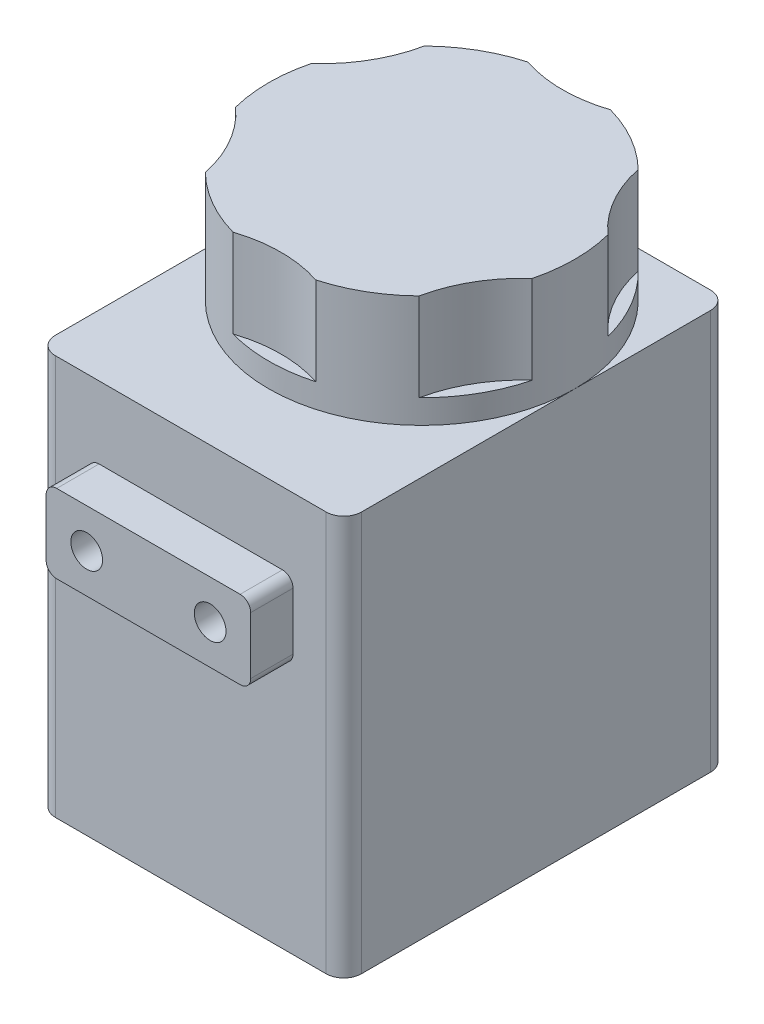
SolidWorks part; units mm, degrees
material "PE High Density"
ref_plane "Front Plane" through (0, 0, 0) normal (0, 0, 1) x (1, 0, 0)
ref_plane "Top Plane" through (0, 0, 0) normal (0, 1, 0) x (1, 0, 0)
ref_plane "Right Plane" through (0, 0, 0) normal (1, 0, 0) x (0, 0, -1)
sketch "Sketch1" plane through (0, 0, 0) normal (0, 1, 0) x (1, 0, 0)
  line L1 (0, 0) -> (22.0472, 0)
  line L2 (0, 0) -> (0, 27.686)
  line L3 (0, 27.686) -> (22.0472, 27.686)
  line L4 (22.0472, 0) -> (22.0472, 27.686)
  dimension "D1" = 22.0472
  dimension "D2" = 27.686
extrude "Boss-Extrude1" add sketch "Sketch1" along normal blind 28.8036
sketch "Sketch2" plane through (0, 0, 0) normal (0, 0, 1) x (1, 0, 0)
  line L0 (0, 20.8026) -> (22.0472, 20.8026) construction
  line L2 (0, 28.8036) -> (0, 0) construction
  line L3 (22.0472, 28.8036) -> (22.0472, 0) construction
  line L4 (0, 28.8036) -> (22.0472, 28.8036) construction
  line L6 (3.6576, 17.9832) -> (18.3896, 17.9832)
  line L7 (3.6576, 17.9832) -> (3.6576, 23.622)
  line L8 (3.6576, 23.622) -> (18.3896, 23.622)
  line L9 (18.3896, 17.9832) -> (18.3896, 23.622)
  line L10 (3.6576, 17.9832) -> (18.3896, 23.622) construction
  line L11 (3.6576, 23.622) -> (18.3896, 17.9832) construction
  point P8 (11.0236, 20.8026)
  dimension "D1" = 8.001
  dimension "D2" = 14.732
  dimension "D3" = 5.6388
extrude "Boss-Extrude2" add sketch "Sketch2" along normal blind 3.048
sketch "Sketch3" plane through (0, 28.8036, 0) normal (0, 1, 0) x (1, 0, 0)
  line L0 (0, 16.637) -> (22.0472, 16.637) construction
  line L1 (0, 27.686) -> (0, 0) construction
  line L2 (22.0472, 0) -> (22.0472, 27.686) construction
  line L3 (22.0472, 27.686) -> (0, 27.686) construction
  circle A0 centre (11.0236, 16.637) radius 11.0236
  dimension "D1" = 11.049
extrude "Boss-Extrude3" add sketch "Sketch3" along normal blind 8.0772
sketch "Sketch4" plane through (0, 36.8808, 0) normal (0, 1, 0) x (1, 0, 0)
  line L0 (11.0236, 27.6606) -> (11.0236, 36.2966) construction
  line L1 (8.1026, 32.307) -> (8.1026, 23.5851) construction
  arc A0 (22.0472, 16.637) -> (0, 16.637) centre (11.0236, 16.637) ccw construction
  circle A1 centre (11.0236, 36.2966) radius 9.525
  circle A2 centre (28.0493, 26.4668) radius 9.525
  circle A3 centre (28.0493, 6.8072) radius 9.525
  circle A4 centre (11.0236, -3.0226) radius 9.525
  circle A5 centre (-6.0021, 6.8072) radius 9.525
  circle A6 centre (-6.0021, 26.4668) radius 9.525
  point P22 (11.0236, 16.637)
  dimension "D2" = 19.05
  dimension "D1" = 2.921
  dimension "D3" = 8.636
  dimension "D4" = 6
extrude "Cut-Extrude1" cut sketch "Sketch4" against normal blind 6.35
fillet "Fillet1" radius 1.27 4 edges at (22.0472, 14.4018, 0) (22.0472, 14.4018, -27.686) (0, 14.4018, -27.686) (0, 14.4018, 0)
fillet "Fillet2" radius 0.762 4 edges at (18.3896, 23.622, 1.524) (3.6576, 17.9832, 1.524) (18.3896, 17.9832, 1.524) (3.6576, 23.622, 1.524)
sketch "Sketch5" plane through (0, 0, 3.048) normal (0, 0, 1) x (1, 0, 0)
  line L0 (3.6576, 20.8026) -> (18.3896, 20.8026) construction
  line L1 (3.6576, 22.86) -> (3.6576, 18.7452) construction
  line L2 (18.3896, 18.7452) -> (18.3896, 22.86) construction
  line L3 (11.0236, 23.622) -> (11.0236, 17.9832) construction
  line L4 (17.6276, 23.622) -> (4.4196, 23.622) construction
  line L5 (4.4196, 17.9832) -> (17.6276, 17.9832) construction
  circle A0 centre (6.5786, 20.8026) radius 1.143
  circle A1 centre (15.4686, 20.8026) radius 1.143
  dimension "D1" = 2.286
  dimension "D2" = 2.921
extrude "Cut-Extrude2" cut sketch "Sketch5" against normal blind 2.54
